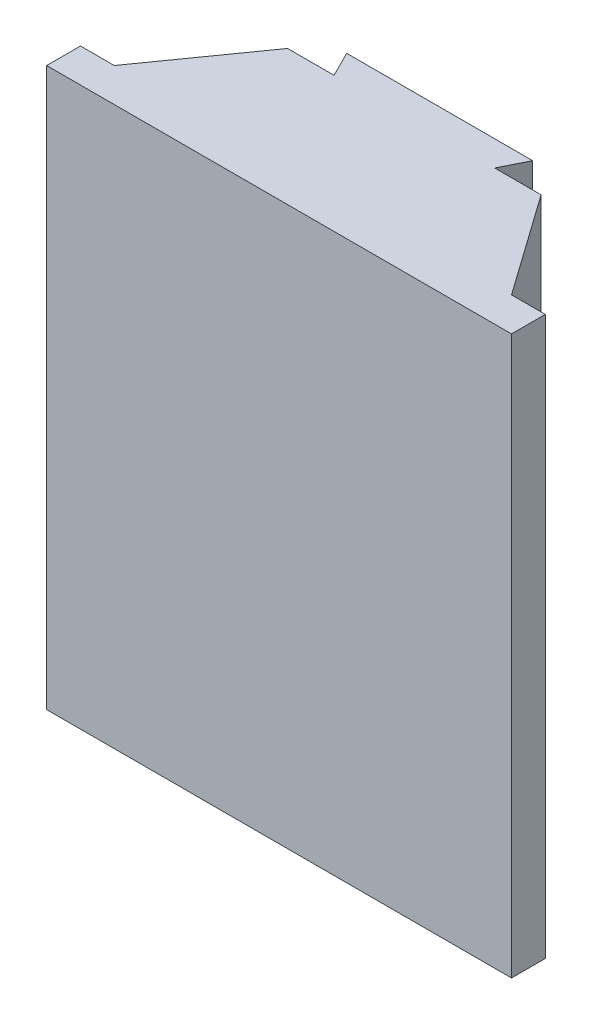
SolidWorks part; units mm, degrees
ref_plane "Front Plane" through (0, 0, 0) normal (0, 0, 1) x (1, 0, 0)
ref_plane "Top Plane" through (0, 0, 0) normal (0, 1, 0) x (1, 0, 0)
ref_plane "Right Plane" through (0, 0, 0) normal (1, 0, 0) x (0, 0, -1)
sketch "Sketch1" plane through (0, 0, 0) normal (0, 1, 0) x (1, 0, 0)
  line L0 (-122.8606, 0) -> (118.0939, 0) construction
  line L1 (0, 63.754) -> (0, -169.06) construction
  line L2 (-137.5, -156) -> (137.5, -156)
  line L3 (137.5, -156) -> (137.5, -136)
  line L4 (-137.5, -136) -> (-117.5, -136)
  line L5 (75, -76) -> (47.5, -76)
  line L6 (47.5, -76) -> (55, -61)
  line L7 (55, -61) -> (-55, -61)
  line L8 (-55, -61) -> (-47.5, -76)
  line L9 (-47.5, -76) -> (-75, -76)
  line L10 (-137.5, -156) -> (-137.5, -136)
  line L11 (-117.5, -136) -> (-75, -76)
  line L12 (137.5, -136) -> (117.5, -136)
  line L13 (117.5, -136) -> (75, -76)
  point P7 (0, -156)
  point P15 (0, -61)
  dimension "D1" = 275
  dimension "D2" = 20
  dimension "D3" = 95
  dimension "D4" = 15
  dimension "D5" = 95
  dimension "D6" = 110
  dimension "D7" = 150
  dimension "D8" = 156
  dimension "D9" = 20
extrude "Boss-Extrude1" add sketch "Sketch1" along normal mid plane 330
